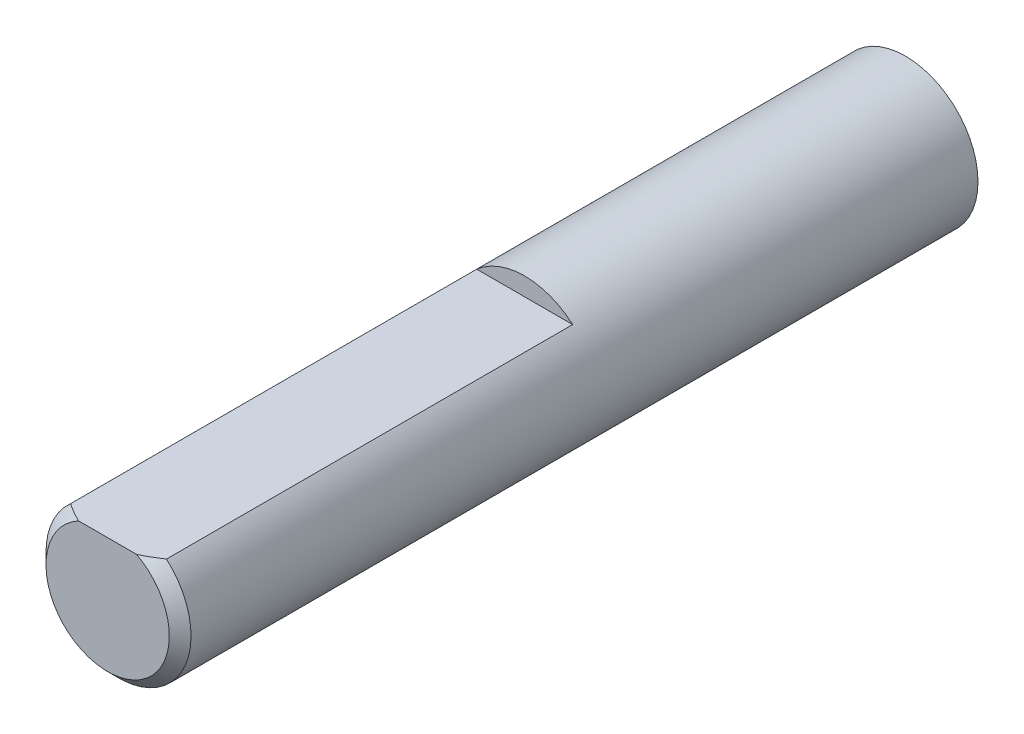
SolidWorks part; units mm, degrees
ref_plane "Plan de face" through (0, 0, 0) normal (0, 0, 1) x (1, 0, 0)
ref_plane "Plan de dessus" through (0, 0, 0) normal (0, 1, 0) x (1, 0, 0)
ref_plane "Plan de droite" through (0, 0, 0) normal (1, 0, 0) x (0, 0, -1)
sketch "Esquisse1" plane through (0, 0, 0) normal (0, 0, 1) x (1, 0, 0)
  circle A0 centre (0, 0) radius 2 construction
  circle A1 centre (0, 0) radius 2
extrude "Boss.-Extru.1" add sketch "Esquisse1" against normal blind 10 and the other way blind 12
chamfer "Chanfrein1" distance 0.3 angle 45 1 edges at (2, 0, 12)
sketch "Esquisse2" plane through (0, 0, 12) normal (0, 0, 1) x (1, 0, 0)
  line L0 (-2.1242, -2) -> (2.0066, -2) construction
  line L1 (-1.3229, 2) -> (1.3229, 2)
  line L2 (-1.3229, 2) -> (-1.3229, 1.5)
  line L3 (-1.3229, 1.5) -> (1.3229, 1.5)
  line L4 (1.3229, 2) -> (1.3229, 1.5)
  circle A0 centre (0, 0) radius 2 construction
  dimension "D1" = 3.5
extrude "Enlèv. mat.-Extru.1" cut sketch "Esquisse2" against normal blind 11.5
